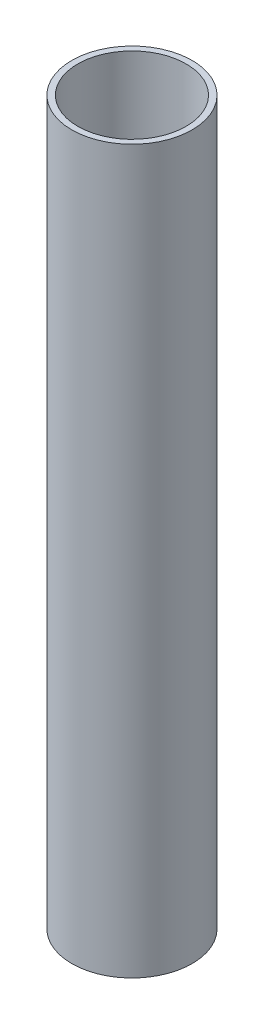
SolidWorks part; units mm, degrees
ref_plane "Front Plane" through (0, 0, 0) normal (0, 0, 1) x (1, 0, 0)
ref_plane "Top Plane" through (0, 0, 0) normal (0, 1, 0) x (1, 0, 0)
ref_plane "Right Plane" through (0, 0, 0) normal (1, 0, 0) x (0, 0, -1)
sketch "Sketch1" plane through (0, 0, 0) normal (0, 1, 0) x (1, 0, 0)
  circle A0 centre (0, 0) radius 25
  circle A1 centre (0, 0) radius 22.5
  dimension "D1" = 45
  dimension "D2" = 50
extrude "Boss-Extrude1" add sketch "Sketch1" along normal blind 300
equation "\"TubeInnerDia\"= 45'Inner tube Diamiter"
equation "\"TubeOuterDia\"= 50'Outer tube dimiter"
equation "\"TubeLength\"= 300'Total length of tube"
